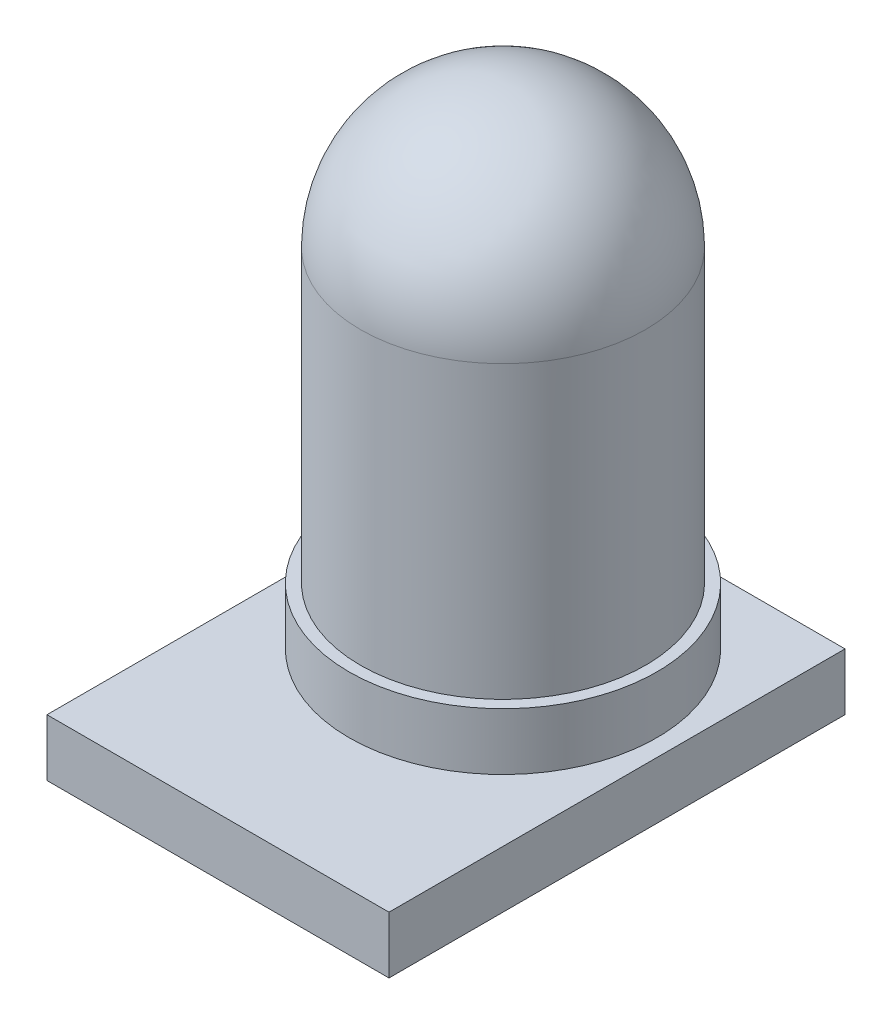
SolidWorks part; units mm, degrees
ref_plane "Front Plane" through (0, 0, 0) normal (0, 0, 1) x (1, 0, 0)
ref_plane "Top Plane" through (0, 0, 0) normal (0, 1, 0) x (1, 0, 0)
ref_plane "Right Plane" through (0, 0, 0) normal (1, 0, 0) x (0, 0, -1)
sketch "Sketch1" plane through (0, 0, 0) normal (0, 1, 0) x (1, 0, 0)
  circle A0 centre (0, 0) radius 2.5
extrude "Boss-Extrude1" add sketch "Sketch1" along normal blind 8.6
fillet "Fillet1" radius 2.5 1 edges at (0, 8.6, 2.5)
sketch "Sketch2" plane through (0, 0, 0) normal (0, -1, 0) x (-1, 0, 0)
  line L3 (0, 3) -> (-3, 3)
  line L4 (-3, 3) -> (-3, -5)
  line L5 (-3, -5) -> (0, -5)
  line L6 (0, -5) -> (3, -5)
  line L7 (3, -5) -> (3, 3)
  line L8 (3, 3) -> (0, 3)
extrude "Boss-Extrude2" add sketch "Sketch2" along normal blind 1
sketch "Sketch3" plane through (0, 0, 0) normal (0, 1, 0) x (1, 0, 0)
  circle A0 centre (0, 0) radius 2.7
extrude "Boss-Extrude3" add sketch "Sketch3" along normal blind 1
